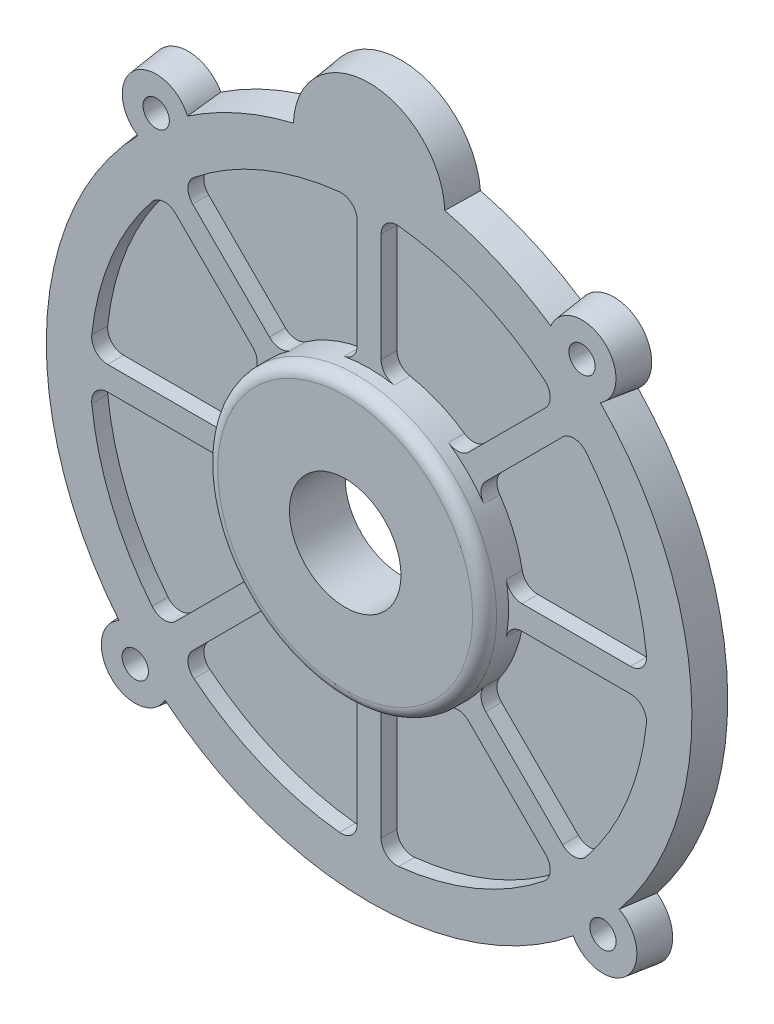
SolidWorks part; units mm, degrees
ref_plane "Front Plane" through (0, 0, 0) normal (0, 0, 1) x (1, 0, 0)
ref_plane "Top Plane" through (0, 0, 0) normal (0, 1, 0) x (1, 0, 0)
ref_plane "Right Plane" through (0, 0, 0) normal (1, 0, 0) x (0, 0, -1)
sketch "Sketch1" plane through (0, 0, 0) normal (0, 0, 1) x (1, 0, 0)
  line L0 (0, 0) -> (0, -41) construction
  line L1 (0, 0) -> (29.3449, -29.3449) construction
  line L2 (0, 0) -> (-29.3449, -29.3449) construction
  line L3 (0, 0) -> (-26.7178, 31.841) construction
  line L4 (0, 0) -> (26.7178, 31.841) construction
  line L5 (0, 0) -> (0, 41) construction
  line L16 (0, 39) -> (-42.0178, 27.7414) construction
  line L17 (0, 39) -> (-50.5, 39) construction
  circle A0 centre (0, 0) radius 12.25
  circle A1 centre (0, 0) radius 41
  circle A2 centre (0, 0) radius 20.5 construction
  circle A3 centre (0, 0) radius 17.5
  circle A4 centre (0, 0) radius 35
  circle A5 centre (-26.7178, 31.841) radius 2.75
  circle A6 centre (-26.7178, 31.841) radius 4.75
  circle A7 centre (26.7178, 31.841) radius 2.75
  circle A8 centre (26.7178, 31.841) radius 4.75
  circle A9 centre (-29.3449, -29.3449) radius 2.75
  circle A10 centre (-29.3449, -29.3449) radius 4.75
  circle A11 centre (29.3449, -29.3449) radius 2.75
  circle A12 centre (29.3449, -29.3449) radius 4.75
  circle A13 centre (0, 0) radius 7
  circle A14 centre (0, 0) radius 6.25
  circle A15 centre (0, 0) radius 4
  circle A16 centre (0, 0) radius 3
  circle A17 centre (0, 39) radius 10
  arc A19 (48.5053, 24.9469) -> (-48.5053, 24.9469) centre (0, 39) ccw construction
  dimension "D5" = 82
  dimension "D6" = 70
  dimension "D7" = 41
  dimension "D8" = 35
  dimension "D9" = 24.5
  dimension "D10" = 14
  dimension "D12" = 8
  dimension "D13" = 6
  dimension "D17" = 39
  dimension "D11" = 12.5
  dimension "D15" = 5.5
  dimension "D16" = 20
  dimension "D3" = 80
sketch "Sketch2" plane through (0, 0, 0) normal (0, 0, 1) x (1, 0, 0)
  circle A0 centre (-26.7178, 31.841) radius 4.75 construction
  circle A1 centre (0, 0) radius 41 construction
  circle A2 centre (26.7178, 31.841) radius 4.75 construction
  circle A3 centre (29.3449, -29.3449) radius 4.75 construction
  circle A4 centre (-29.3449, -29.3449) radius 4.75 construction
  arc A5 (-22.6, 34.2088) -> (-29.7646, 28.1969) centre (-26.7178, 31.841) ccw
  arc A6 (-29.7646, 28.1969) -> (-32.1158, -25.4868) centre (0, 0) ccw
  arc A7 (29.7646, 28.1969) -> (22.6, 34.2088) centre (26.7178, 31.841) ccw
  arc A8 (25.4868, -32.1158) -> (32.1158, -25.4868) centre (29.3449, -29.3449) ccw
  arc A9 (-32.1158, -25.4868) -> (-25.4868, -32.1158) centre (-29.3449, -29.3449) ccw
  arc A10 (22.6, 34.2088) -> (9.9704, 39.7692) centre (0, 0) ccw
  arc A11 (32.1158, -25.4868) -> (29.7646, 28.1969) centre (0, 0) ccw
  arc A12 (-25.4868, -32.1158) -> (25.4868, -32.1158) centre (0, 0) ccw
  circle A13 centre (0, 39) radius 10 construction
  arc A14 (9.9704, 39.7692) -> (-9.9704, 39.7692) centre (0, 39) ccw
  arc A15 (-9.9704, 39.7692) -> (-22.6, 34.2088) centre (0, 0) ccw
extrude "Boss-Extrude1" add sketch "Sketch2" along normal blind 4 draft 7 from offset 4 offset against normal yes
sketch "Sketch4" plane through (0, 0, 0) normal (0, 0, 1) x (1, 0, 0)
  line L0 (-13.3895, -11.2682) -> (-25.7867, -23.6653)
  line L1 (0, 0) -> (-29.3449, -29.3449) construction
  line L2 (0, 0) -> (-29.3449, -29.3449) construction
  line L4 (0, 0) -> (-41, 0) construction
  line L5 (-34.9678, -1.5) -> (-17.4356, -1.5)
  circle A0 centre (0, 0) radius 17.5 construction
  circle A1 centre (0, 0) radius 35 construction
  arc A2 (-17.4356, -1.5) -> (-13.3895, -11.2682) centre (0, 0) ccw
  arc A3 (-34.9678, -1.5) -> (-25.7867, -23.6653) centre (0, 0) ccw
  circle A4 centre (0, 0) radius 41 construction
  dimension "D1" = 1.5
  dimension "D2" = 1.5
extrude "Cut-Extrude1" cut sketch "Sketch4" against normal blind 2
fillet "Fillet1" radius 2 4 edges at (-25.7867, -23.6653, -1) (-13.3895, -11.2682, -1) (-17.4356, -1.5, -1) (-34.9678, -1.5, -1)
pattern_circular "CirPattern1" count 8 over 360 about axis through (0, 0, 0) along (0, 0, 1) of "Cut-Extrude1", "Fillet1"
sketch "Sketch5" plane through (0, 0, 0) normal (0, 0, 1) x (1, 0, 0)
  point P0 (-29.3449, -29.3449)
  point P1 (-26.7178, 31.841)
  point P3 (26.7178, 31.841)
  point P5 (29.3449, -29.3449)
hole_wizard "M4x0.7 Tapped Hole1" positions "Sketch8" profile "Sketch7" tap size "M4x0.7" standard "ANSI Metric" end condition through all
sketch "Sketch8" plane through (0, 0, -4) normal (0, 0, -1) x (-1, 0, 0)
  point P0 (26.7178, 31.841)
  point P3 (29.3449, -29.3449)
  point P6 (-29.3449, -29.3449)
  point P9 (-26.7178, 31.841)
sketch "Sketch7" plane through (-26.7178, 31.841, -4) normal (1, 0, 0) x (0, 1, 0)
  line L0 (0, 0) -> (0, 4)
  line L1 (0, 4) -> (1.65, 4)
  line L2 (1.65, 4) -> (1.65, 0)
  line L5 (1.65, 0) -> (0, 0)
  line L11 (0, -6.35) -> (0, 107.95) construction
  dimension "Thread Major Dia." = 3.3
  dimension "Thru Tap Drill Depth" = 4
sketch "Sketch9" plane through (0, 0, 0) normal (0, 0, 1) x (1, 0, 0)
  circle A0 centre (0, 0) radius 17.5 construction
  circle A1 centre (0, 0) radius 17.5
extrude "Boss-Extrude2" add sketch "Sketch9" along normal blind 3
fillet "Fillet2" radius 1.5 1 edges at (17.5, 0, 3)
sketch "Sketch10" plane through (0, 0, 3) normal (0, 0, 1) x (1, 0, 0)
  point P0 (0, 0)
hole_wizard "Ø14.0 (14) Diameter Hole1" positions "Sketch12" profile "Sketch11" hole size "Ø14.0" standard "ANSI Metric" end condition through all
sketch "Sketch12" plane through (0, 0, 3) normal (0, 0, 1) x (1, 0, 0)
  point P0 (0, 0)
sketch "Sketch11" plane through (0, 0, 3) normal (1, 0, 0) x (0, -1, 0)
  line L0 (0, 0) -> (0, 7)
  line L1 (0, 7) -> (7, 7)
  line L2 (7, 7) -> (7, 0)
  line L5 (7, 0) -> (0, 0)
  line L11 (0, -6.35) -> (0, 107.95) construction
  dimension "Thru Hole Dia." = 14
  dimension "Thru Hole Depth" = 7
